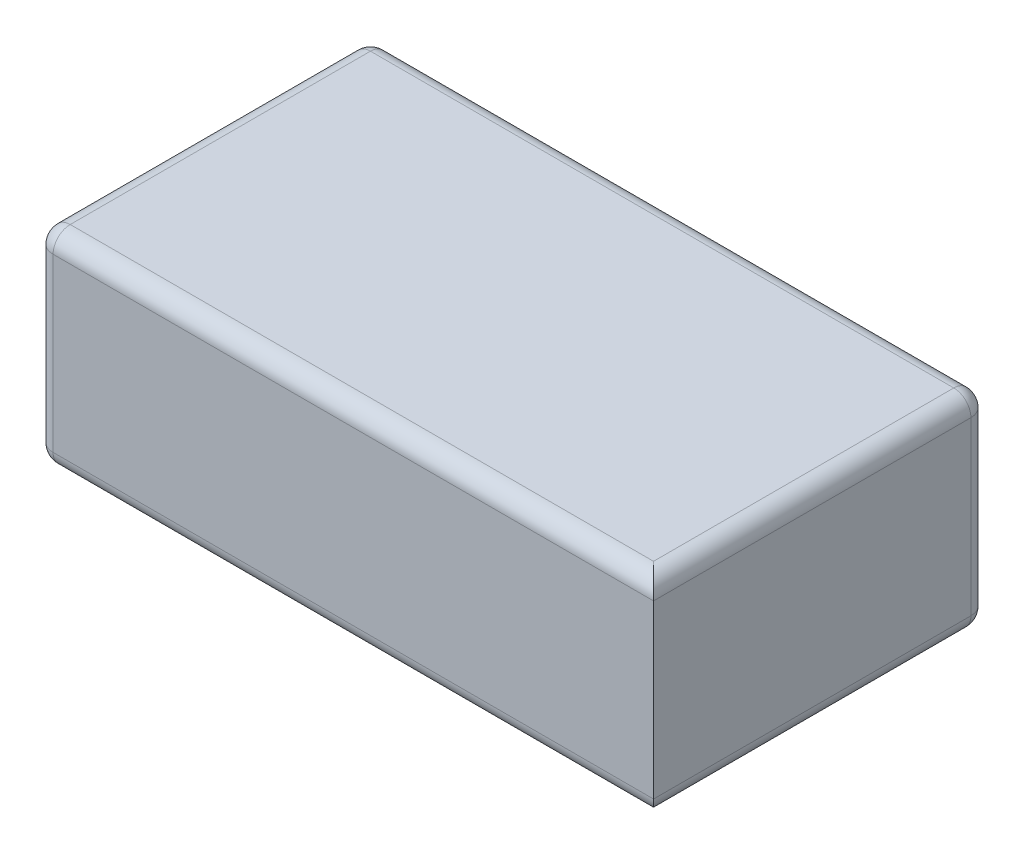
SolidWorks part; units mm, degrees
ref_plane "Plan de face" through (0, 0, 0) normal (0, 0, 1) x (1, 0, 0)
ref_plane "Plan de dessus" through (0, 0, 0) normal (0, 1, 0) x (1, 0, 0)
ref_plane "Plan de droite" through (0, 0, 0) normal (1, 0, 0) x (0, 0, -1)
sketch "Esquisse1" plane through (0, 0, 0) normal (0, 1, 0) x (1, 0, 0)
  line L1 (0, 0) -> (72, 0)
  line L2 (0, 0) -> (0, 39)
  line L3 (0, 39) -> (72, 39)
  line L4 (72, 0) -> (72, 39)
  dimension "D1" = 72
  dimension "D2" = 39
extrude "Extrusion2" add sketch "Esquisse1" along normal blind 24
fillet "Congé3" radius 2 11 edges at (36, 0, 0) (72, 0, -19.5) (72, 24, -19.5) (36, 24, 0) (0, 24, -19.5) (0, 12, 0) (0, 0, -19.5) (72, 12, -39) (36, 24, -39) (0, 12, -39) (36, 0, -39)
